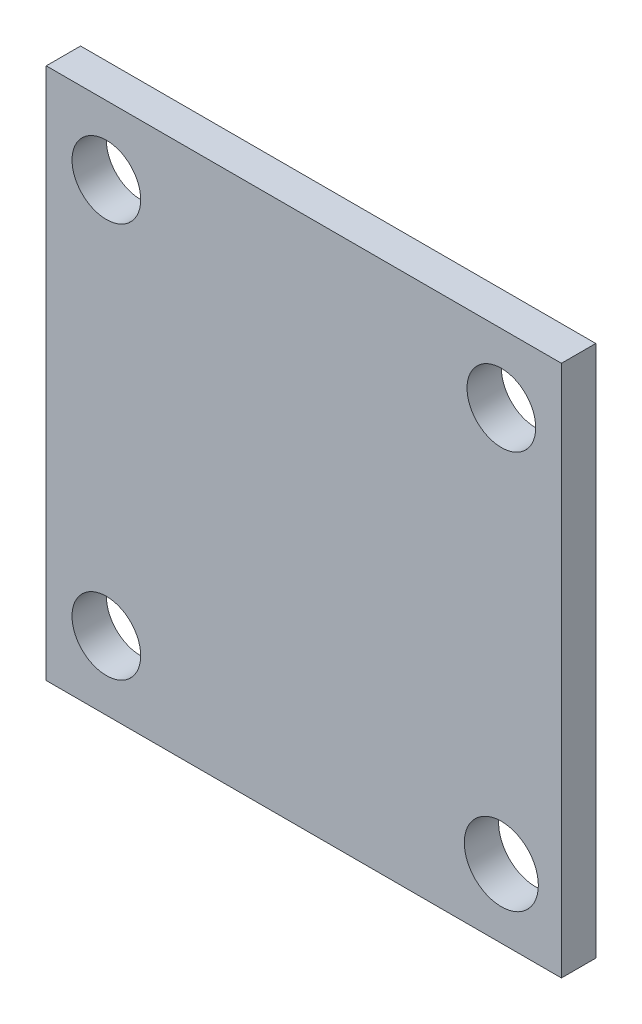
SolidWorks part; units mm, degrees
ref_plane "Front Plane" through (0, 0, 0) normal (0, 0, 1) x (1, 0, 0)
ref_plane "Top Plane" through (0, 0, 0) normal (0, 1, 0) x (1, 0, 0)
ref_plane "Right Plane" through (0, 0, 0) normal (1, 0, 0) x (0, 0, -1)
sketch "Sketch2" plane through (0, 0, 0) normal (0, 0, 1) x (1, 0, 0)
  line L0 (15.0011, -15.5011) -> (-15.0011, -15.5011)
  line L1 (15.0011, -15.5011) -> (15.0011, 15.5011)
  line L2 (15.0011, 15.5011) -> (-15.0011, 15.5011)
  line L3 (-15.0011, -15.5011) -> (-15.0011, 15.5011)
  circle A0 centre (-11.4989, 11.5033) radius 2
  circle A1 centre (11.5033, 11.5011) radius 2
  circle A2 centre (-11.5011, -11.4989) radius 2
  circle A3 centre (11.5011, -11.5011) radius 2.1563
  dimension "D1" = 4
  dimension "D2" = 4
  dimension "D3" = 4
  dimension "D4" = 4.3125
extrude "Boss-Extrude1" add sketch "Sketch2" along normal blind 2
